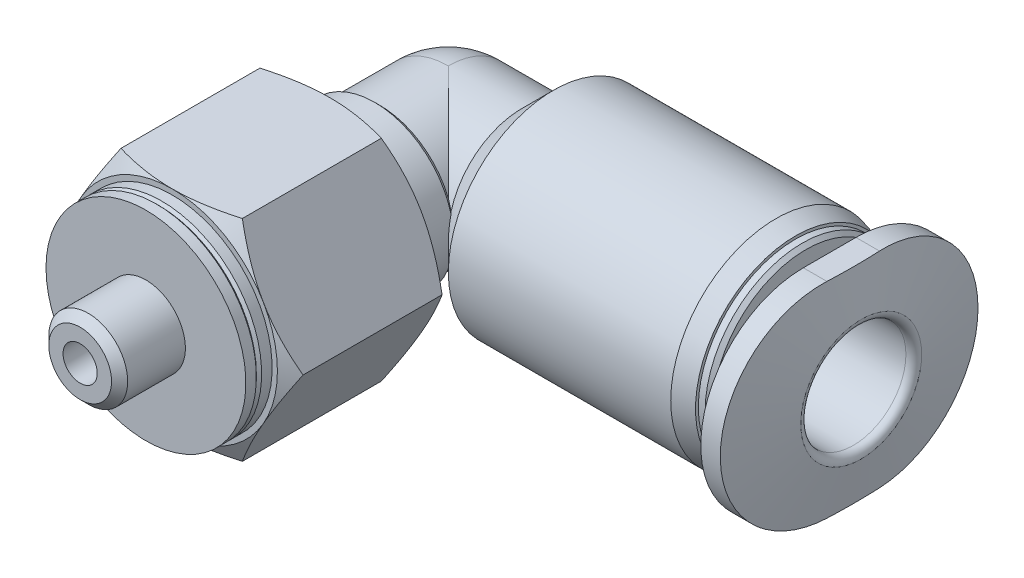
SolidWorks part; units mm, degrees
ref_plane "Front Plane" through (0, 0, 0) normal (0, 0, 1) x (1, 0, 0)
ref_plane "Top Plane" through (0, 0, 0) normal (0, 1, 0) x (1, 0, 0)
ref_plane "Right Plane" through (0, 0, 0) normal (1, 0, 0) x (0, 0, -1)
ref_plane "Plane1" through (0, 0, 0) normal (0, 0, 1) x (1, 0, 0)
sketch "Sketch1" plane through (0, 0, 0) normal (0, 0, 1) x (1, 0, 0)
  line L0 (0, 2.8) -> (2.8, 2.8)
  line L1 (2.8, 2.8) -> (4, 4)
  line L2 (4, 4) -> (12.4571, 4)
  line L3 (12.4571, 4) -> (13.2, 3.801)
  line L4 (13.2, 3.801) -> (13.2, 3.6938)
  line L5 (13.2, 3.6938) -> (13.4586, 3.6938)
  line L6 (13.4586, 3.6938) -> (13.6, 3.5524)
  line L7 (13.6, 3.5524) -> (13.6, 2.5)
  line L8 (13.6, 2.5) -> (14.13, 2.5)
  line L9 (14.5, 2.87) -> (14.5, 5.9)
  line L10 (14.5, 5.9) -> (14.8974, 5.9)
  line L11 (15.0944, 5.7347) -> (15.7, 2.3)
  line L12 (15.7, 2.3) -> (15.7, 0)
  line L13 (15.7, 0) -> (-2.8, 0)
  line L14 (15.7, 0) -> (-2.8, 0) construction
  arc A0 (-2.8, 0) -> (0, 2.8) centre (0, 0) cw
  arc A1 (14.13, 2.5) -> (14.5, 2.87) centre (14.13, 2.87) ccw
  arc A2 (14.8974, 5.9) -> (15.0944, 5.7347) centre (14.8974, 5.7) cw
revolve "Revolve1" add sketch "Sketch1" angle 360 about L14
ref_plane "Plane2" through (0, 0, 0) normal (1, 0, 0) x (0, 0, -1)
sketch "Sketch2" plane through (0, 0, 0) normal (1, 0, 0) x (0, 0, -1)
  line L0 (-11.5, 0) -> (-11.5, 3.8)
  line L1 (-11.5, 3.8) -> (-11.1, 3.8)
  line L2 (-11.1, 3.8) -> (-11, 3.7)
  line L3 (-11, 3.7) -> (-10.9, 3.8)
  line L4 (-10.9, 3.8) -> (-10.5, 3.8)
  line L5 (-10.5, 3.8) -> (-10.5, 4)
  line L6 (-10.5, 4) -> (-10.1305, 4.64)
  line L7 (-10.1305, 4.64) -> (-4.8695, 4.64)
  line L8 (-4.8695, 4.64) -> (-4.5, 4)
  line L9 (-4.5, 4) -> (-4.5, 3)
  line L10 (-4.5, 3) -> (-2.8, 3)
  line L11 (-2.8, 3) -> (-2.6, 2.8)
  line L12 (-2.6, 2.8) -> (0, 2.8)
  line L13 (0, 2.8) -> (0, 0)
  line L14 (0, 0) -> (-11.5, 0)
  line L15 (0, 0) -> (-11.5, 0) construction
revolve "Revolve2" add sketch "Sketch2" angle 360 about L15
ref_plane "Plane3" through (0, 0, 0) normal (1, 0, 0) x (0, 0, -1)
sketch "Sketch3" plane through (0, 0, 0) normal (1, 0, 0) x (0, 0, -1)
  line L0 (-14, 0) -> (-14, 1.1935)
  line L1 (-14, 1.1935) -> (-13.6935, 1.5)
  line L2 (-13.6935, 1.5) -> (-11.5, 1.5)
  line L3 (-11.5, 1.5) -> (-11.5, 0)
  line L4 (-11.5, 0) -> (-14, 0)
  line L5 (-11.5, 0) -> (-14, 0) construction
revolve "Revolve3" add sketch "Sketch3" angle 360 about L5
cosmetic thread "Cosmetic Thread1" parameters "D1"=2.5, "D2"=2.387
ref_plane "Plane4" through (15.7, 0, 0) normal (1, 0, 0) x (0, 0, -1)
sketch "Sketch4" plane through (15.7, 0, 0) normal (1, 0, 0) x (0, 0, -1)
  line L0 (-9.8, -5.658) -> (0, -11.3161)
  line L1 (0, -11.3161) -> (9.8, -5.658)
  line L2 (9.8, -5.658) -> (9.8, 5.658)
  line L3 (9.8, 5.658) -> (0, 11.3161)
  line L4 (0, 11.3161) -> (-9.8, 5.658)
  line L5 (-9.8, 5.658) -> (-9.8, -5.658)
  line L6 (-1, -3.9) -> (1, -3.9)
  line L7 (1, 3.9) -> (-1, 3.9)
  arc A0 (-1, 3.9) -> (-1, -3.9) centre (-1, 0) ccw
  arc A1 (1, -3.9) -> (1, 3.9) centre (1, 0) ccw
extrude "Cut-Extrude1" cut sketch "Sketch4" against normal blind 1.2
ref_plane "Plane5" through (0, 0, 0) normal (1, 0, 0) x (0, 0, -1)
sketch "Sketch5" plane through (0, 0, 0) normal (1, 0, 0) x (0, 0, -1)
  line L0 (-14, 0) -> (-14, 0.65)
  line L1 (-14, 0.65) -> (0, 0.65)
  line L2 (0, 0.65) -> (0, 0)
  line L3 (0, 0) -> (-14, 0)
  line L4 (0, 0) -> (-14, 0) construction
revolve "Cut-Revolve1" cut sketch "Sketch5" angle 360 about L4
ref_plane "Plane6" through (0, 0, 0) normal (0, 1, 0) x (1, 0, 0)
sketch "Sketch6" plane through (0, 0, 0) normal (0, 1, 0) x (1, 0, 0)
  line L0 (0, 0.65) -> (4.1, 0.65)
  line L1 (4.1, 0.65) -> (4.1, 2)
  line L2 (4.1, 2) -> (15.4, 2)
  line L3 (15.7, 2.3) -> (15.7, 0)
  line L4 (15.7, 0) -> (-0.65, 0)
  line L5 (15.7, 0) -> (-0.65, 0) construction
  arc A0 (-0.65, 0) -> (0, 0.65) centre (0, 0) cw
  arc A1 (15.4, 2) -> (15.7, 2.3) centre (15.4, 2.3) ccw
revolve "Cut-Revolve2" cut sketch "Sketch6" angle 360 about L5
ref_plane "Plane7" through (0, 0, 11.5) normal (0, 0, 1) x (1, 0, 0)
sketch "Sketch7" plane through (0, 0, 11.5) normal (0, 0, 1) x (1, 0, 0)
  line L0 (-8, -8) -> (8, -8)
  line L1 (8, -8) -> (8, 8)
  line L2 (8, 8) -> (-8, 8)
  line L3 (-8, 8) -> (-8, -8)
  line L4 (-4.6188, 0) -> (-2.3094, -4)
  line L5 (-2.3094, -4) -> (2.3094, -4)
  line L6 (2.3094, -4) -> (4.6188, 0)
  line L7 (4.6188, 0) -> (2.3094, 4)
  line L8 (2.3094, 4) -> (-2.3094, 4)
  line L9 (-2.3094, 4) -> (-4.6188, 0)
extrude "Cut-Extrude2" cut sketch "Sketch7" against normal blind 7.0556
